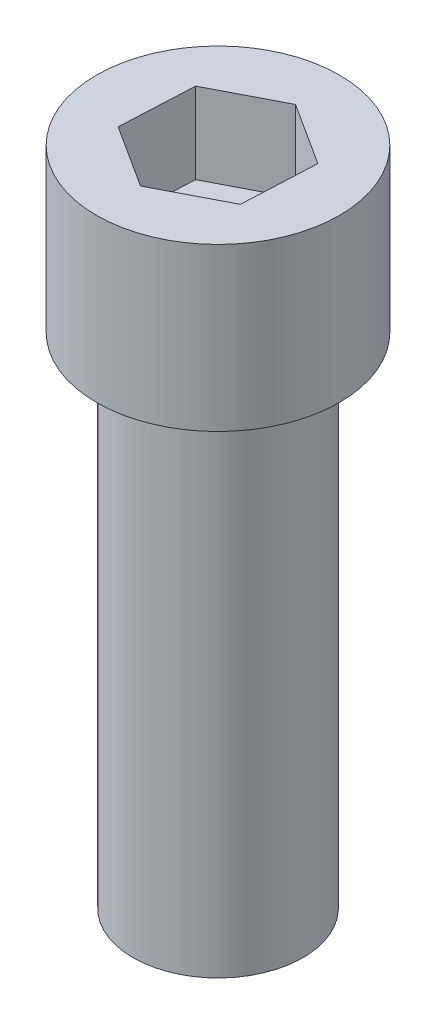
SolidWorks part; units mm, degrees
material "Aço carbono simples"
ref_plane "Plano frontal" through (0, 0, 0) normal (0, 0, 1) x (1, 0, 0)
ref_plane "Plano superior" through (0, 0, 0) normal (0, 1, 0) x (1, 0, 0)
ref_plane "Plano direito" through (0, 0, 0) normal (1, 0, 0) x (0, 0, -1)
sketch "Esboço1" plane through (0, 0, 0) normal (0, 1, 0) x (1, 0, 0)
  circle A0 centre (0, 0) radius 5.25
  dimension "D1" = 10.5
extrude "Ressalto-extrusão1" add sketch "Esboço1" along normal blind 34.8
sketch "Esboço2" plane through (0, 34.8, 0) normal (0, 1, 0) x (1, 0, 0)
  circle A0 centre (0, 0) radius 7.5
  dimension "D1" = 15
extrude "Ressalto-extrusão2" add sketch "Esboço2" along normal blind 10
sketch "Esboço3" plane through (0, 44.8, 0) normal (0, 1, 0) x (1, 0, 0)
  line L1 (0.2125, 4.5697) -> (-3.8512, 2.4689)
  line L2 (-3.8512, 2.4689) -> (-4.0638, -2.1008)
  line L3 (-4.0638, -2.1008) -> (-0.2125, -4.5697)
  line L4 (-0.2125, -4.5697) -> (3.8512, -2.4689)
  line L5 (3.8512, -2.4689) -> (4.0638, 2.1008)
  line L6 (4.0638, 2.1008) -> (0.2125, 4.5697)
  circle A0 centre (0, 0) radius 3.9618 construction
extrude "Corte-extrusão1" cut sketch "Esboço3" against normal blind 5
sketch "Esboço4" plane through (0, 0, 0) normal (0, -1, 0) x (1, 0, 0)
  circle A0 centre (0, 0) radius 5.25
extrude "Corte-extrusão2" cut sketch "Esboço4" against normal blind 4
